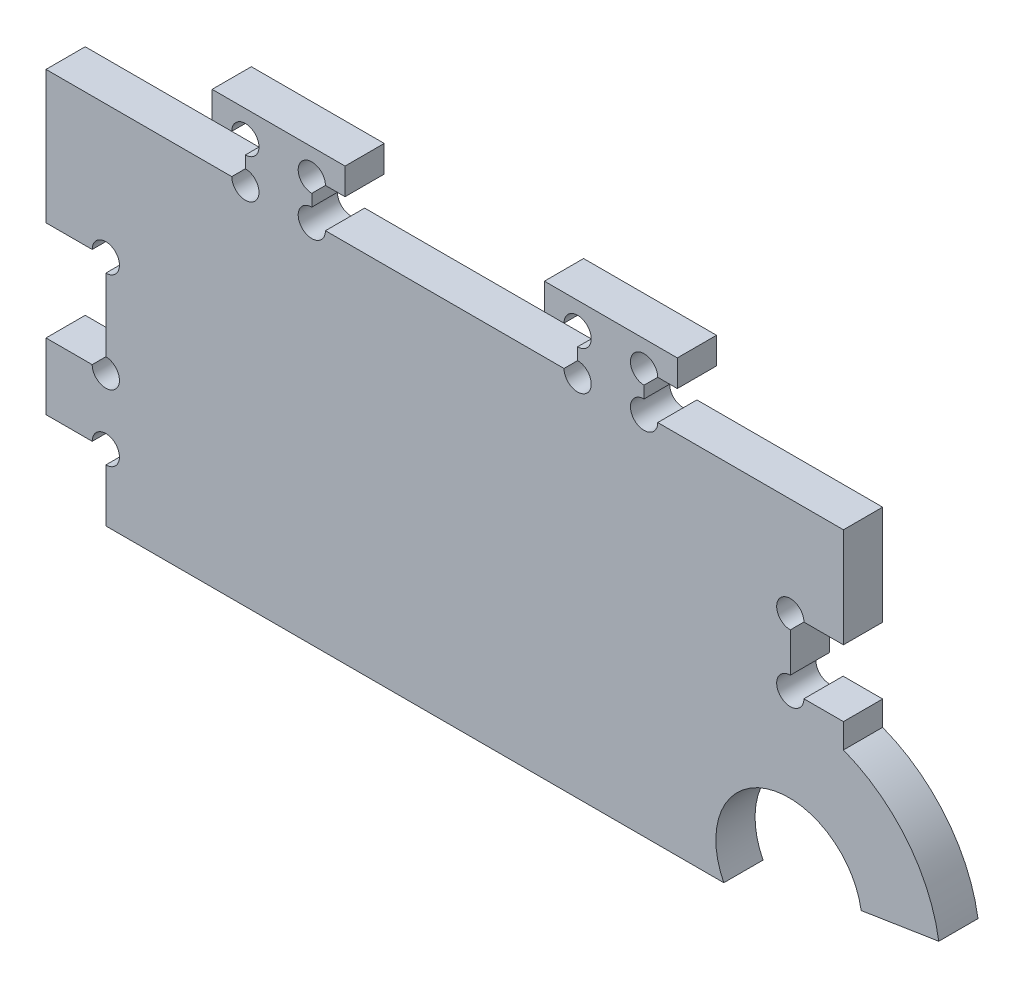
SolidWorks part; units mm, degrees
ref_plane "Front Plane" through (0, 0, 0) normal (0, 0, 1) x (1, 0, 0)
ref_plane "Top Plane" through (0, 0, 0) normal (0, 1, 0) x (1, 0, 0)
ref_plane "Right Plane" through (0, 0, 0) normal (1, 0, 0) x (0, 0, -1)
sketch "Sketch1" plane through (0, 0, 0) normal (0, 0, 1) x (1, 0, 0)
  line L0 (-17.6033, 83.9872) -> (76.3967, 83.9872) construction
  line L1 (86.1956, 88.9853) -> (94.3967, 110.2893) construction
  line L2 (86.1956, 88.9853) -> (108.746, 92.535) construction
  line L3 (76.3967, 83.9872) -> (-17.6033, 83.9872)
  line L4 (-17.6033, 83.9872) -> (-17.6033, 138.9872)
  line L5 (-17.6033, 138.9872) -> (94.3967, 138.9872)
  line L6 (94.3967, 138.9872) -> (94.3967, 110.2893)
  line L7 (108.746, 92.535) -> (97.0618, 90.6958)
  arc A0 (108.746, 92.535) -> (94.3967, 110.2893) centre (86.1956, 88.9853) ccw
  arc A1 (97.0618, 90.6958) -> (76.3967, 83.9872) centre (86.1956, 88.9853) ccw
  arc A2 (72.0509, 71.0676) -> (86.3967, 66.1582) centre (86.1956, 88.9853) ccw construction
  dimension "D1" = 60
  dimension "D2" = 112
  dimension "D3" = 55
  dimension "D4" = 90
extrude "Boss-Extrude1" add sketch "Sketch1" along normal blind 5.9 contours A1 L7 A0 L6 L5 L4 L3
sketch "Sketch2" plane through (0, 0, 5.9) normal (0, 0, 1) x (1, 0, 0)
  line L0 (76.3967, 83.9872) -> (-17.6033, 83.9872) construction
  line L1 (-17.6033, 138.9872) -> (-25.6033, 138.9872)
  line L2 (-17.6033, 138.9872) -> (-17.6033, 83.9872)
  line L3 (-17.6033, 83.9872) -> (-25.6033, 83.9872)
  line L4 (-25.6033, 138.9872) -> (-25.6033, 83.9872)
  dimension "D1" = 8
extrude "Boss-Extrude2" add sketch "Sketch2" against normal up to surface (5.9 mm away) up to face at (62.0343, 107.6425, 0)
sketch "Sketch3" plane through (0, 0, 5.9) normal (0, 0, 1) x (1, 0, 0)
  line L0 (-25.6033, 138.9872) -> (-25.6033, 83.9872) construction
  line L1 (-25.6033, 118.9872) -> (-16.6033, 118.9872)
  line L2 (-25.6033, 118.9872) -> (-25.6033, 103.9872)
  line L3 (-25.6033, 103.9872) -> (-16.6033, 103.9872)
  line L4 (-16.6033, 118.9872) -> (-16.6033, 103.9872)
  line L5 (-25.6033, 138.9872) -> (-25.6033, 83.9872) construction
  line L7 (94.3967, 123.9872) -> (86.3967, 123.9872)
  line L8 (94.3967, 123.9872) -> (94.3967, 113.9872)
  line L9 (94.3967, 113.9872) -> (86.3967, 113.9872)
  line L10 (86.3967, 123.9872) -> (86.3967, 113.9872)
  line L11 (94.3967, 138.9872) -> (94.3967, 110.2893) construction
  line L12 (76.3967, 83.9872) -> (-25.6033, 83.9872) construction
  line L13 (-25.6033, 93.9872) -> (-16.6033, 93.9872)
  line L14 (-25.6033, 93.9872) -> (-25.6033, 83.9872)
  line L15 (-25.6033, 83.9872) -> (-16.6033, 83.9872)
  line L16 (-16.6033, 93.9872) -> (-16.6033, 83.9872)
  line L18 (-25.6033, 138.9872) -> (94.3967, 138.9872) construction
  point P6 (-16.6033, 111.4872)
  point P11 (-25.6033, 111.4872)
  dimension "D1" = 15
  dimension "D3" = 10
  dimension "D4" = 8
  dimension "D5" = 0
  dimension "D6" = 9
  dimension "D7" = 10
  dimension "D8" = 15
extrude "Cut-Extrude1" cut sketch "Sketch3" against normal through all
sketch "Sketch4" plane through (0, 0, 5.9) normal (0, 0, 1) x (1, 0, 0)
  line L0 (4.3967, 138.9872) -> (4.3967, 144.8872)
  line L1 (-25.6033, 138.9872) -> (94.3967, 138.9872) construction
  line L2 (4.3967, 144.8872) -> (-0.6033, 144.8872)
  line L3 (-0.6033, 144.8872) -> (-0.6033, 148.8872)
  line L4 (-0.6033, 148.8872) -> (19.3967, 148.8872)
  line L5 (19.3967, 148.8872) -> (19.3967, 144.8872)
  line L6 (19.3967, 144.8872) -> (14.3967, 144.8872)
  line L7 (14.3967, 144.8872) -> (14.3967, 138.9872)
  line L8 (14.3967, 138.9872) -> (4.3967, 138.9872)
  line L9 (49.3967, 144.8872) -> (49.3967, 148.8872)
  line L10 (69.3967, 148.8872) -> (69.3967, 144.8872)
  line L11 (49.3967, 148.8872) -> (69.3967, 148.8872)
  line L12 (54.3967, 144.8872) -> (49.3967, 144.8872)
  line L13 (69.3967, 144.8872) -> (64.3967, 144.8872)
  line L14 (64.3967, 144.8872) -> (64.3967, 138.9872)
  line L15 (64.3967, 138.9872) -> (54.3967, 138.9872)
  line L16 (54.3967, 138.9872) -> (54.3967, 144.8872)
  line L17 (-25.6033, 138.9872) -> (-25.6033, 118.9872) construction
  point P4 (9.3967, 148.8872)
  point P11 (9.3967, 138.9872)
  dimension "D1" = 5.9
  dimension "D2" = 10
  dimension "D3" = 20
  dimension "D4" = 4
  dimension "D6" = 30
  dimension "D5" = 2
extrude "Boss-Extrude3" add sketch "Sketch4" against normal up to surface (5.9 mm away) up to face at (38.9534, 109.6099, 0)
sketch "Sketch5" plane through (0, 0, 5.9) normal (0, 0, 1) x (1, 0, 0)
  circle A0 centre (-16.6033, 93.9872) radius 2.05
  circle A1 centre (-16.6033, 103.9872) radius 2.05
  circle A2 centre (-16.6033, 118.9872) radius 2.05
  circle A3 centre (4.3967, 138.9872) radius 2.05
  circle A4 centre (14.3967, 138.9872) radius 2.05
  circle A5 centre (14.3967, 144.8872) radius 2.05
  circle A6 centre (4.3967, 144.8872) radius 2.05
  circle A7 centre (54.3967, 144.8872) radius 2.05
  circle A8 centre (64.3967, 144.8872) radius 2.05
  circle A9 centre (64.3967, 138.9872) radius 2.05
  circle A10 centre (54.3967, 138.9872) radius 2.05
  circle A11 centre (86.3967, 123.9872) radius 2.05
  circle A12 centre (86.3967, 113.9872) radius 2.05
  dimension "D1" = 4.1
extrude "Cut-Extrude2" cut sketch "Sketch5" against normal up to next
equation "\"e\" = 5.9"
equation "\"D1@Sketch4\"= \"e\""
equation "\"D1@Boss-Extrude1\"=\"e\""
